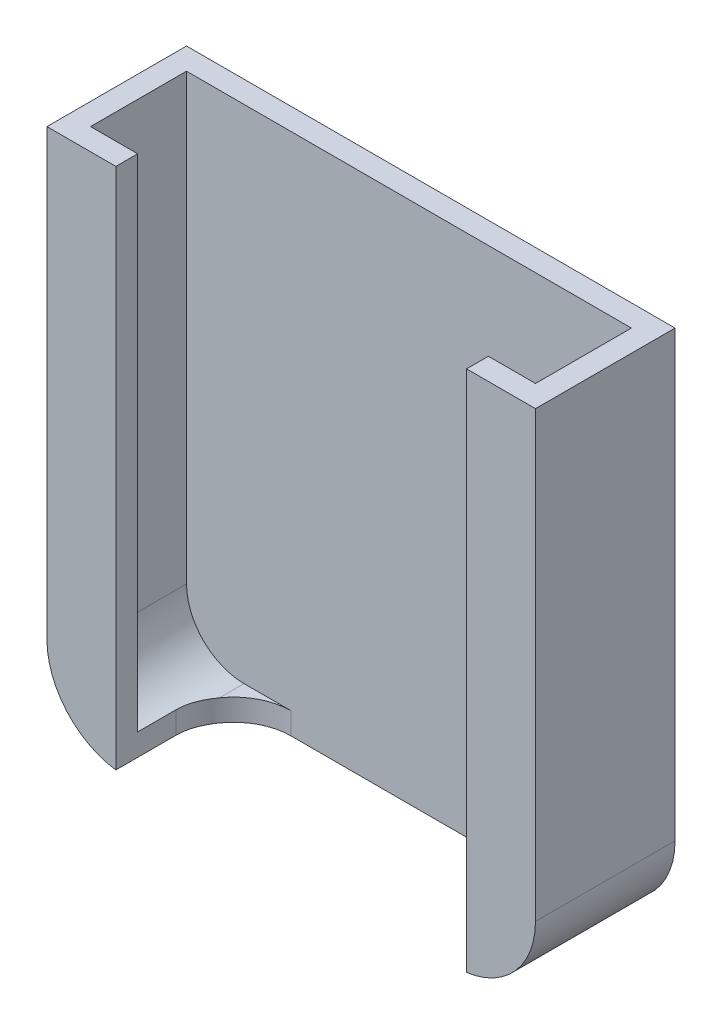
SolidWorks part; units mm, degrees
ref_plane "Front Plane" through (0, 0, 0) normal (0, 0, 1) x (1, 0, 0)
ref_plane "Top Plane" through (0, 0, 0) normal (0, 1, 0) x (1, 0, 0)
ref_plane "Right Plane" through (0, 0, 0) normal (1, 0, 0) x (0, 0, -1)
sketch "Sketch1" plane through (0, 0, 0) normal (0, 0, 1) x (1, 0, 0)
  line L1 (0, 0) -> (71.12, 0)
  line L2 (0, 0) -> (0, 76.2)
  line L3 (0, 76.2) -> (71.12, 76.2)
  line L4 (71.12, 0) -> (71.12, 76.2)
  dimension "D1" = 71.12
  dimension "D2" = 76.2
extrude "Boss-Extrude1" add sketch "Sketch1" along normal mid plane 20.32
sketch "Sketch2" plane through (0, 76.2, 0) normal (0, 1, 0) x (1, 0, 0)
  line L0 (3.175, 6.985) -> (67.945, 6.985)
  line L1 (67.945, 6.985) -> (67.945, -6.985)
  line L2 (3.175, -6.985) -> (67.945, -6.985)
  line L3 (71.12, -10.16) -> (0, -10.16) construction
  line L8 (3.175, -6.985) -> (3.175, 6.985)
  line L9 (71.12, 10.16) -> (0, 10.16) construction
  line L10 (0, -10.16) -> (0, 10.16) construction
  line L11 (71.12, -10.16) -> (71.12, 10.16) construction
  line L12 (35.56, 16.362) -> (35.56, -10.4064) construction
  point P17 (35.56, 6.985)
  dimension "D1" = 3.175
  dimension "D2" = 3.175
  dimension "D3" = 3.175
  dimension "D4" = 3.175
extrude "Cut-Extrude1" cut sketch "Sketch2" against normal offset from surface (73.025 mm away) 3.175 up to face at (35.56, 0, 0)
hole_wizard "CSK for 1/4 Flat Head Socket Cap Screw1" positions "Sketch8" profile "Sketch9" countersink size "1/4" standard "ANSI Inch"
sketch "Sketch8" plane through (0, 0, -6.985) normal (0, 0, 1) x (1, 0, 0)
  line L1 (35.56, 76.2) -> (35.56, 28.3115) construction
  line L3 (67.945, 76.2) -> (3.175, 76.2) construction
  line L4 (3.175, 3.175) -> (67.945, 3.175) construction
  point P0 (25.6871, 53.975)
  point P2 (45.4329, 53.975)
  point P4 (45.4329, 41.275)
  point P6 (25.6871, 41.275)
  point P20 (35.56, 76.2)
  dimension "D1" = 19.7459
  dimension "D2" = 12.7
  dimension "D3" = 38.1
sketch "Sketch9" plane through (25.6871, 53.975, -6.985) normal (1, 0, 0) x (0, -1, 0)
  line L0 (0, 0) -> (0, 3.175)
  line L1 (0, 3.175) -> (3.429, 3.175)
  line L2 (3.429, 3.175) -> (3.429, 4.0671)
  line L3 (3.429, 4.0671) -> (6.9645, 0)
  line L5 (6.9645, 0) -> (0, 0)
  line L6 (-3.429, 4.0671) -> (-6.9645, 0) construction
  line L11 (0, -6.35) -> (0, 107.95) construction
  dimension "Thru Hole Dia." = 6.858
  dimension "Thru Hole Depth" = 3.175
  dimension "Near C'Sink Dia." = 13.929
  dimension "Near C'Sink Angle" = 82
sketch "Sketch10" plane through (0, 76.2, 0) normal (0, 1, 0) x (1, 0, 0)
  line L1 (71.12, -10.16) -> (0, -10.16) construction
  line L2 (10.033, -10.16) -> (61.087, -10.16)
  line L3 (10.033, -10.16) -> (10.033, 6.985)
  line L4 (10.033, 6.985) -> (61.087, 6.985)
  line L6 (61.087, -10.16) -> (61.087, 6.985)
  line L7 (67.945, 6.985) -> (3.175, 6.985) construction
  line L8 (35.56, 22.4709) -> (35.56, -29.2083) construction
  line L9 (71.12, 10.16) -> (0, 10.16) construction
  point P12 (35.56, 10.16)
  dimension "D1" = 51.054
extrude "Cut-Extrude2" cut sketch "Sketch10" against normal through all
fillet "Fillet5" radius 8.382 2 edges at (10.033, 1.5875, -6.985) (61.087, 1.5875, -6.985)
fillet "Fillet3" radius 8.382 2 edges at (67.945, 3.175, 0) (3.175, 3.175, 0)
sketch "Sketch11" plane through (0, 0, 10.16) normal (0, 0, 1) x (1, 0, 0)
  line L0 (0, 11.557) -> (0, 0)
  line L1 (0, 0) -> (11.557, 0)
  line L2 (71.12, 0) -> (71.12, 76.2) construction
  line L3 (71.12, 11.557) -> (71.12, 0)
  line L4 (61.087, 0) -> (71.12, 0) construction
  line L5 (59.563, 0) -> (71.12, 0)
  arc A0 (59.563, 3.175) -> (67.945, 11.557) centre (59.563, 11.557) ccw construction
  arc A1 (59.563, 3.175) -> (67.945, 11.557) centre (59.563, 11.557) ccw construction
  arc A2 (3.175, 11.557) -> (11.557, 3.175) centre (11.557, 11.557) ccw construction
  arc A3 (3.175, 11.557) -> (11.557, 3.175) centre (11.557, 11.557) ccw construction
  arc A4 (59.563, 0) -> (71.12, 11.557) centre (59.563, 11.557) ccw
  arc A5 (0, 11.557) -> (11.557, 0) centre (11.557, 11.557) ccw
extrude "Cut-Extrude3" cut sketch "Sketch11" against normal through all
equation "\"width\"= 2.53in'Phone width"
equation "\"D1@Sketch1\" = \"width\" + 2 * \"wall\" +2*\"margin\"'Overall width of holster"
equation "\"wall\"= 0.125in'Metal thickness"
equation "\"height\"= 3in'Overall holster height"
equation "\"D2@Sketch1\"= \"height\"'Overall holster height"
equation "\"depth\"= 0.53in'Thickness of phone"
equation "\"D1@Boss-Extrude1\"= \"depth\" + 2 * \"wall\" + 2*\"margin\" 'Overal depth of holster"
equation "\"D3@Sketch2\"=\"wall\""
equation "\"D4@Sketch2\"= \"wall\""
equation "\"screen_width\"= 2.01in'Width of visible screen"
equation "\"margin\"= 0.01in'Slop to allow the phone to fit properly"
equation "\"D2@Sketch2\" = \"wall\""
equation "\"D1@Sketch2\"=\"wall\""
equation "\"D1@Cut-Extrude1\"=\"wall\""
equation "\"lower_edge\"= .408'How deep the phone sits in the holster"
equation "\"tool_diam\"= .66'Diameter of the tool used for undercuts, set to match the corners of the phone"
equation "\"button_cutout\"= .48in'Cutout for the iPhone button"
equation "\"D1@Fillet3\" = \"tool_diam\"/2 ' fillets where the corners of the phone sit"
